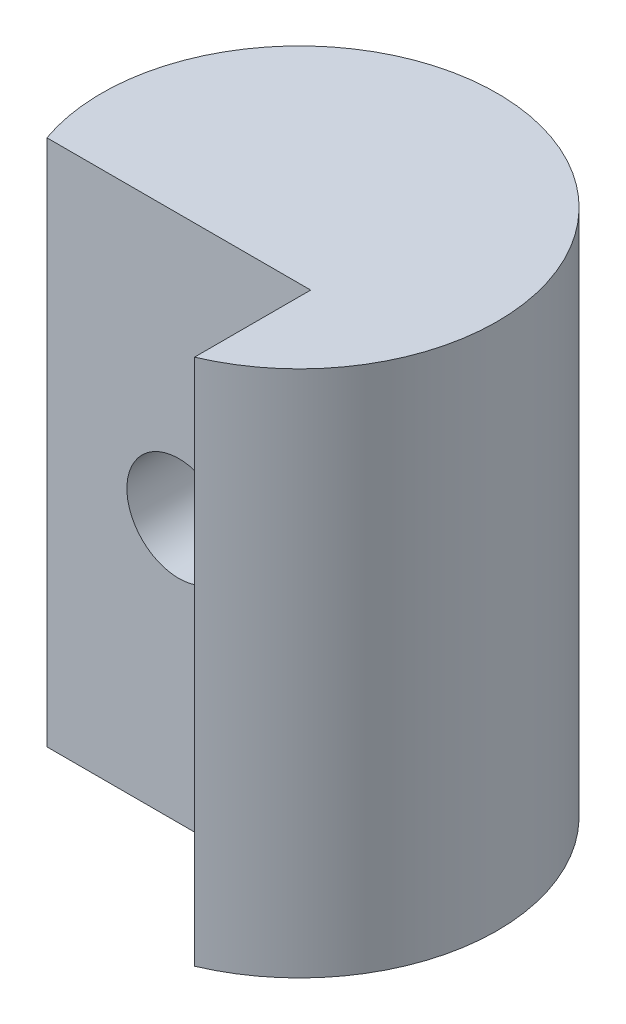
SolidWorks part; units mm, degrees
ref_plane "Top Plane" through (0, 0, 0) normal (0, 0, 1) x (1, 0, 0)
ref_plane "Front Plane" through (0, 0, 0) normal (0, 1, 0) x (1, 0, 0)
ref_plane "Right Plane" through (0, 0, 0) normal (1, 0, 0) x (0, 0, -1)
sketch "Profile Sketch" plane through (0, 0, 0) normal (0, 1, 0) x (1, 0, 0)
  circle A0 centre (0, 0) radius 4.7625
  dimension "D1" = 9.525
extrude "Boss-Extrude1" add sketch "Profile Sketch" along normal blind 12.7
sketch "Plate Relief Sketch" plane through (0, 0, 0) normal (0, -1, 0) x (1, 0, 0)
  line L1 (1.8599, 1.5875) -> (-4.4901, 1.5875)
  line L2 (1.8599, 1.5875) -> (1.8599, 4.7625)
  line L3 (1.8599, 4.7625) -> (-4.4901, 4.7625)
  line L4 (-4.4901, 1.5875) -> (-4.4901, 4.7625)
  circle A1 centre (0, 0) radius 4.7625 construction
  dimension "D1" = 3.175
  dimension "D2" = 6.35
extrude "Plate Relief Cut" cut sketch "Plate Relief Sketch" against normal up to next
sketch "Screw Mounting Sketch" plane through (0, 0, 1.5875) normal (0, 0, 1) x (1, 0, 0)
  line L0 (-1.3151, 12.7) -> (-1.3151, 0) construction
  line L1 (-4.4901, 0) -> (1.8599, 0) construction
  line L2 (-4.4901, 12.7) -> (1.8599, 12.7) construction
  line L6 (-4.7625, 0) -> (4.7625, 0) construction
  line L7 (-4.7625, 0) -> (4.7625, 0) construction
  point P2 (-1.3151, 6.35)
  dimension "D1" = 3.175
hole_wizard "M3x0.5 Tapped Hole1" positions "3DSketch2" profile "Sketch2" tap size "M3x0.5" standard "ANSI Metric" end condition through all
sketch3d "3DSketch2"
  point P0 (-1.3151, 6.35, 1.5875)
sketch "Sketch2" plane through (-1.3151, 6.35, 1.5875) normal (1, 0, 0) x (0, -1, 0)
  line L0 (0, 0) -> (0, 6.35)
  line L1 (0, 6.35) -> (1.25, 6.35)
  line L2 (1.25, 6.35) -> (1.25, 0)
  line L5 (1.25, 0) -> (0, 0)
  line L11 (0, -6.35) -> (0, 107.95) construction
  dimension "Thru Tap Drill Dia." = 2.5
  dimension "Thru Tap Drill Depth" = 6.35
cosmetic thread "Hole Thread1" parameters "D2"=3
